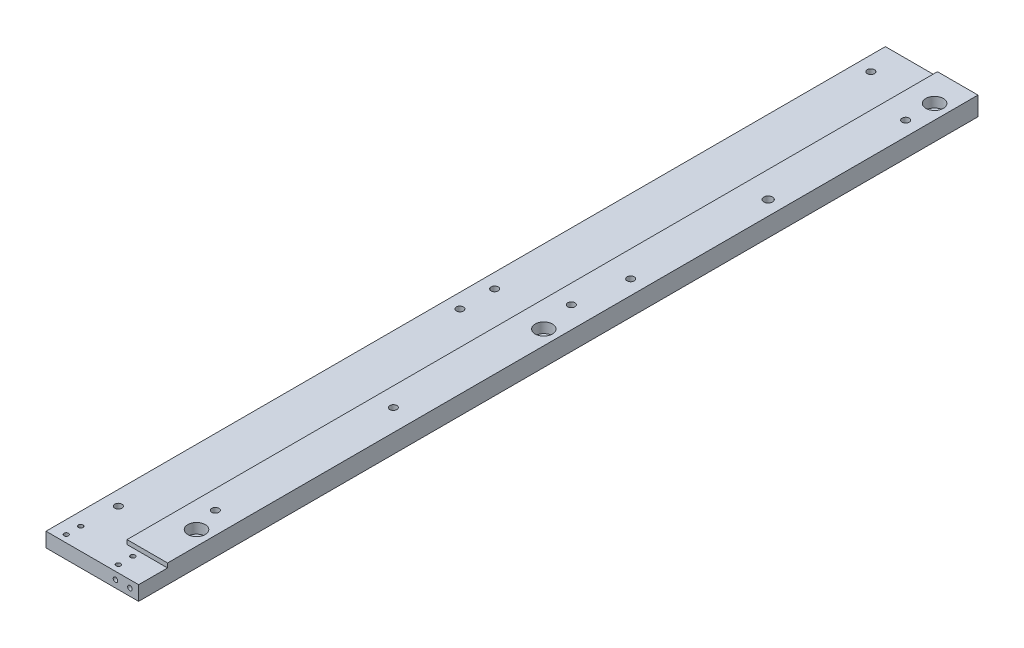
SolidWorks part; units mm, degrees
ref_plane "Front Plane" through (0, 0, 0) normal (0, 0, 1) x (1, 0, 0)
ref_plane "Top Plane" through (0, 0, 0) normal (0, 1, 0) x (1, 0, 0)
ref_plane "Right Plane" through (0, 0, 0) normal (1, 0, 0) x (0, 0, -1)
sketch "Sketch1" plane through (0, 0, 0) normal (0, 0, 1) x (1, 0, 0)
  line L1 (-16, -2.5) -> (16, -2.5)
  line L2 (-16, -2.5) -> (-16, 2.5)
  line L3 (-16, 2.5) -> (16, 2.5)
  line L4 (16, -2.5) -> (16, 2.5)
  line L5 (-16, -2.5) -> (16, 2.5) construction
  line L6 (-16, 2.5) -> (16, -2.5) construction
  point P0 (0, 0)
  dimension "D1" = 32
  dimension "D2" = 5
extrude "Boss-Extrude1" add sketch "Sketch1" along normal blind 290
sketch "Sketch2" plane through (0, 2.5, 0) normal (0, 1, 0) x (1, 0, 0)
  line L0 (16, -290) -> (-16, -290) construction
  line L1 (16, 0) -> (2, 0)
  line L2 (16, 0) -> (16, -280)
  line L3 (16, -280) -> (2, -280)
  line L4 (2, 0) -> (2, -280)
  dimension "D1" = 14
  dimension "D2" = 10
extrude "Boss-Extrude2" add sketch "Sketch2" along normal blind 1.5
sketch "Sketch3" plane through (0, 4, 0) normal (0, 1, 0) x (1, 0, 0)
  line L0 (16, -280) -> (16, 0) construction
  line L1 (16, 0) -> (2, 0) construction
  circle A0 centre (11, -10) radius 3
  circle A1 centre (11, -145) radius 3
  circle A2 centre (11, -265) radius 3
  dimension "D1" = 5
  dimension "D2" = 6
  dimension "D3" = 10
  dimension "D4" = 135
  dimension "D5" = 120
extrude "Cut-Extrude1" cut sketch "Sketch3" against normal blind 3.5
sketch "Sketch4" plane through (0, 0.5, 0) normal (0, 1, 0) x (1, 0, 0)
  circle A0 centre (11, -10) radius 1.75
  circle A1 centre (11, -145) radius 1.75
  circle A2 centre (11, -265) radius 1.75
  dimension "D1" = 3.5
extrude "Cut-Extrude2" cut sketch "Sketch4" against normal through all
sketch "Sketch5" plane through (0, 2.5, 0) normal (0, 1, 0) x (1, 0, 0)
  line L0 (-16, -290) -> (-16, 0) construction
  line L1 (16, -290) -> (-16, -290) construction
  circle A0 centre (-11.5, -282.5) radius 0.785
  circle A1 centre (6.5, -282.5) radius 0.785
  circle A2 centre (-11.5, -287.5) radius 0.785
  circle A3 centre (6.5, -287.5) radius 0.785
  dimension "D3" = 1.57
  dimension "D5" = 2.5
  dimension "D1" = 18
  dimension "D2" = 5
  dimension "D4" = 4.5
extrude "Cut-Extrude3" cut sketch "Sketch5" against normal through all
sketch "Sketch6" plane through (0, 4, 0) normal (0, 1, 0) x (1, 0, 0)
  line L0 (16, -280) -> (16, 0) construction
  line L1 (16, 0) -> (2, 0) construction
  circle A0 centre (11, -20) radius 1.23
  dimension "D1" = 2.46
  dimension "D2" = 5
  dimension "D3" = 20
extrude "Cut-Extrude4" cut sketch "Sketch6" against normal through all
pattern_linear "LPattern1" count 2 spacing 95 along (0, 0, 1) of "Cut-Extrude4"
sketch "Sketch7" plane through (0, -2.5, 0) normal (0, -1, 0) x (1, 0, 0)
  line L0 (-16, 290) -> (-16, 0) construction
  line L1 (-16, 290) -> (16, 290) construction
  line L2 (-16, 0) -> (16, 0) construction
  circle A0 centre (-11, 10) radius 1.23
  circle A1 centre (-11, 140) radius 1.23
  circle A2 centre (-11, 152) radius 1.23
  circle A3 centre (-11, 270) radius 1.23
  point P12 (0, 0)
  point P13 (0, 0)
  point P14 (0, 0)
  dimension "D1" = 2.46
  dimension "D2" = 5
  dimension "D3" = 20
  dimension "D4" = 2.46
  dimension "D6" = 5
  dimension "D8" = 10
  dimension "D5" = 12
  dimension "D7" = 138
extrude "Cut-Extrude5" cut sketch "Sketch7" against normal through all
sketch "Sketch8" plane through (0, -2.5, 0) normal (0, -1, 0) x (1, 0, 0)
  line L0 (16, 290) -> (16, 0) construction
  line L1 (-16, 0) -> (16, 0) construction
  circle A0 centre (8.5, 133) radius 1.23
  point P8 (0, 0)
  point P9 (0, 0)
  dimension "D1" = 2.46
  dimension "D2" = 7.5
  dimension "D3" = 133
extrude "Cut-Extrude6" cut sketch "Sketch8" against normal through all
pattern_linear "LPattern2" count 3 spacing 61.5 along (0, 0, 1) of "Cut-Extrude6"
sketch "Sketch9" plane through (0, -2.5, 0) normal (0, -1, 0) x (1, 0, 0)
  line L0 (16, 290) -> (16, 0) construction
  circle A0 centre (11, 67.5) radius 1.5
  circle A1 centre (11, 20) radius 1.23 construction
  dimension "D1" = 3
  dimension "D2" = 5
  dimension "D3" = 47.5
extrude "Cut-Extrude7" cut sketch "Sketch9" against normal through all
sketch "Sketch10" plane through (0, 0, 290) normal (0, 0, 1) x (1, 0, 0)
  line L0 (16, -2.5) -> (16, 2.5) construction
  circle A0 centre (13, 0) radius 0.785
  circle A1 centre (8, 0) radius 0.785
  point P4 (0, 0)
  point P7 (0, 0)
  dimension "D1" = 1.57
  dimension "D3" = 3
  dimension "D2" = 5
extrude "Cut-Extrude8" cut sketch "Sketch10" against normal blind 8
